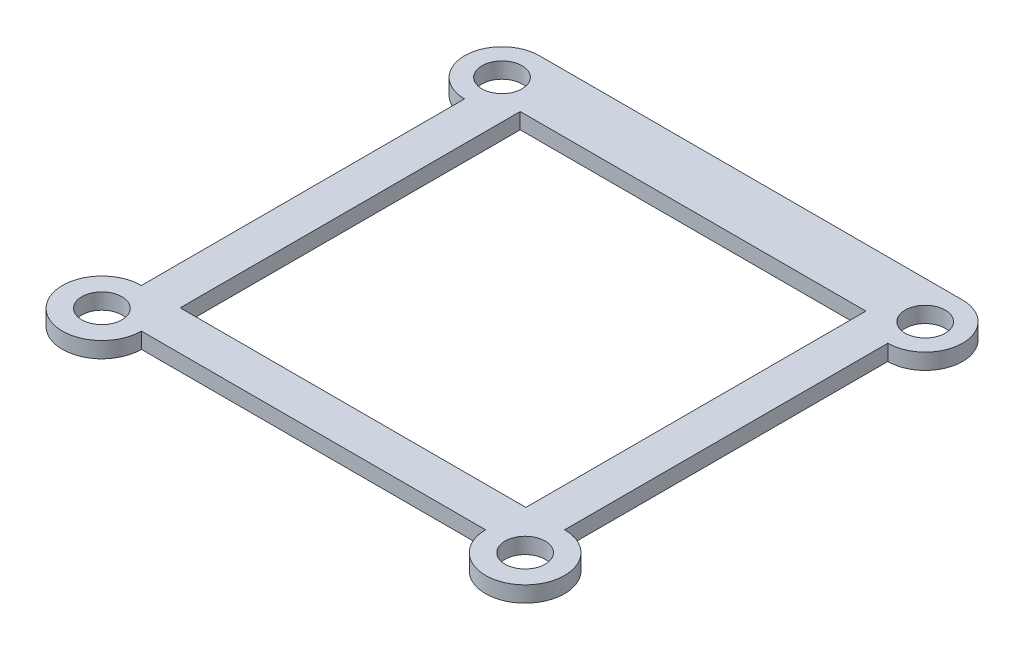
SolidWorks part; units mm, degrees
ref_plane "Front Plane" through (0, 0, 0) normal (0, 0, 1) x (1, 0, 0)
ref_plane "Top Plane" through (0, 0, 0) normal (0, 1, 0) x (1, 0, 0)
ref_plane "Right Plane" through (0, 0, 0) normal (1, 0, 0) x (0, 0, -1)
sketch "Sketch2" plane through (0, 0, 0) normal (0, 1, 0) x (1, 0, 0)
  line L0 (9.83, 96.9117) -> (9.83, 6.4505) construction
  line L1 (-5.42, 46.569) -> (25.08, 46.569)
  line L2 (-5.42, 46.569) -> (-5.42, 16.569)
  line L3 (-5.42, 16.569) -> (25.08, 16.569)
  line L4 (25.08, 46.569) -> (25.08, 16.569)
  line L6 (-8.84, 51.6811) -> (28.5, 51.6811)
  line L7 (-8.84, 45.0811) -> (-8.84, 16.569)
  line L8 (28.5, 45.0811) -> (28.5, 16.569)
  line L9 (-5.3521, 13.0811) -> (25.0121, 13.0811)
  circle A0 centre (-8.84, 48.3811) radius 1.77
  circle A1 centre (28.5, 48.3811) radius 1.77
  circle A2 centre (-8.84, 13.0811) radius 1.77
  circle A3 centre (28.5, 13.0811) radius 1.77
  arc A4 (28.5, 51.6811) -> (28.5, 45.0811) centre (28.5, 48.3811) cw
  arc A5 (-8.84, 51.6811) -> (-8.84, 45.0811) centre (-8.84, 48.3811) ccw
  arc A6 (-8.84, 16.569) -> (-5.3521, 13.0811) centre (-8.84, 13.0811) ccw
  arc A7 (28.5, 16.569) -> (25.0121, 13.0811) centre (28.5, 13.0811) cw
  point P19 (9.83, 51.6811)
  point P23 (24.5178, -2.5866)
  point P28 (0, 0)
  point P29 (-4.9295, -2.5866)
  point P30 (0, 0)
  dimension "D1" = 30
  dimension "D2" = 30.5
extrude "Boss-Extrude1" add sketch "Sketch2" along normal blind 1.4
